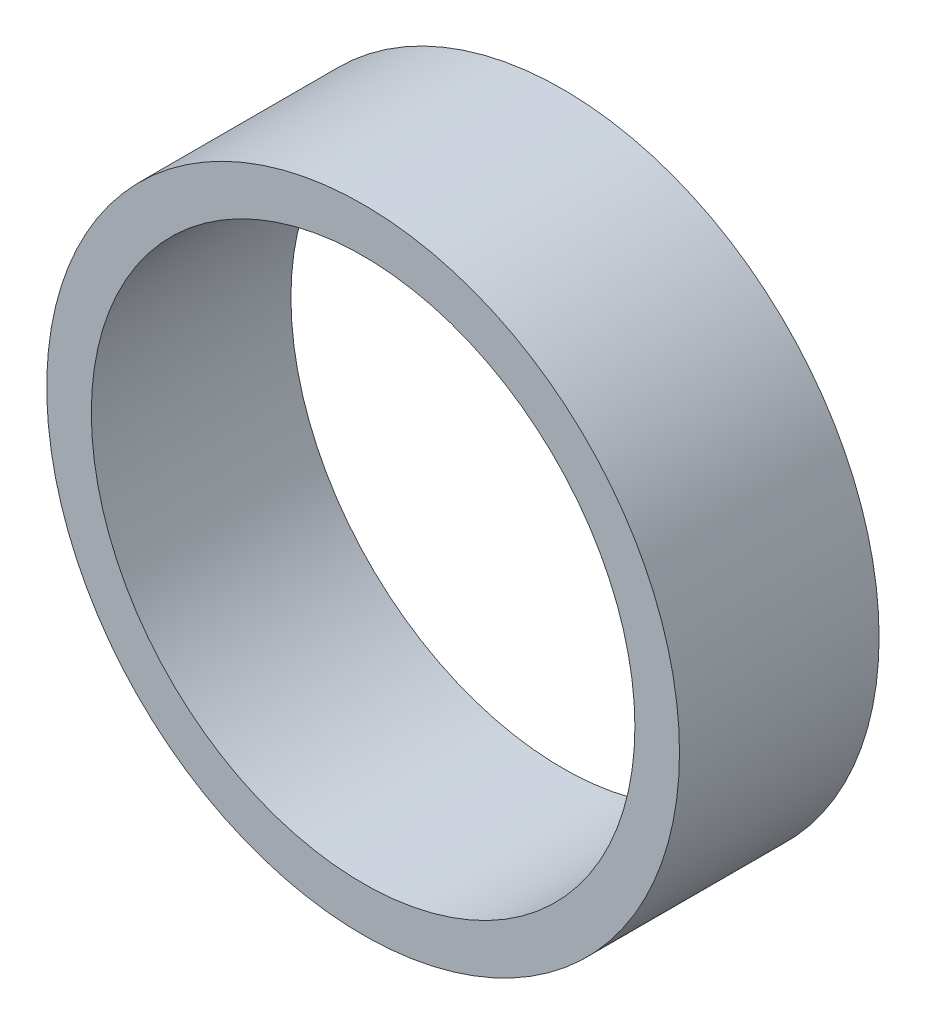
SolidWorks part; units mm, degrees
ref_plane "Front Plane" through (0, 0, 0) normal (0, 0, 1) x (1, 0, 0)
ref_plane "Top Plane" through (0, 0, 0) normal (0, 1, 0) x (1, 0, 0)
ref_plane "Right Plane" through (0, 0, 0) normal (1, 0, 0) x (0, 0, -1)
sketch "Sketch1" plane through (0, 0, 0) normal (0, 0, 1) x (1, 0, 0)
  circle A0 centre (0, 0) radius 6.4
  circle A1 centre (0, 0) radius 7.45
  dimension "D1" = 14.9
  dimension "D2" = 12.8
extrude "Boss-Extrude1" add sketch "Sketch1" along normal blind 4.7
